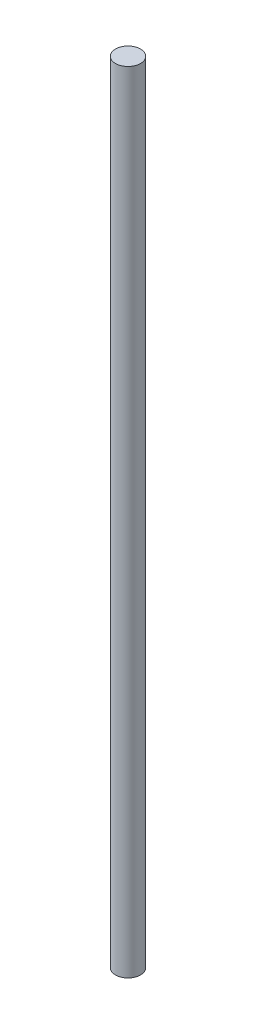
SolidWorks part; units mm, degrees
material "Acrylic (Medium-high impact)"
ref_plane "Front Plane" through (0, 0, 0) normal (0, 0, 1) x (1, 0, 0)
ref_plane "Top Plane" through (0, 0, 0) normal (0, 1, 0) x (1, 0, 0)
ref_plane "Right Plane" through (0, 0, 0) normal (1, 0, 0) x (0, 0, -1)
sketch "Sketch1" plane through (0, 0, 0) normal (0, 1, 0) x (1, 0, 0)
  circle A0 centre (0, 0) radius 3.175
  dimension "D1" = 6.35
extrude "Boss-Extrude1" add sketch "Sketch1" along normal blind 200.025
hole_wizard "#32 (0.116) Diameter Hole2" positions "Sketch4" profile "Sketch5" hole size "#32" standard "ANSI Inch"
sketch "Sketch4" plane through (0, 0, 0) normal (0, -1, 0) x (-1, 0, 0)
  point P0 (0, 0)
sketch "Sketch5" plane through (0, 0, 0) normal (1, 0, 0) x (0, 0, -1)
  line L0 (0, 0) -> (0, 4.5428)
  line L1 (0, 4.5428) -> (1.4732, 3.6576)
  line L2 (1.4732, 3.6576) -> (1.4732, 0)
  line L5 (1.4732, 0) -> (0, 0)
  line L10 (0, 4.5428) -> (-1.4732, 3.6576) construction
  line L11 (0, -6.35) -> (0, 107.95) construction
  dimension "Hole Dia." = 2.9464
  dimension "Hole Depth" = 3.6576
  dimension "Drill Angle" = 118
